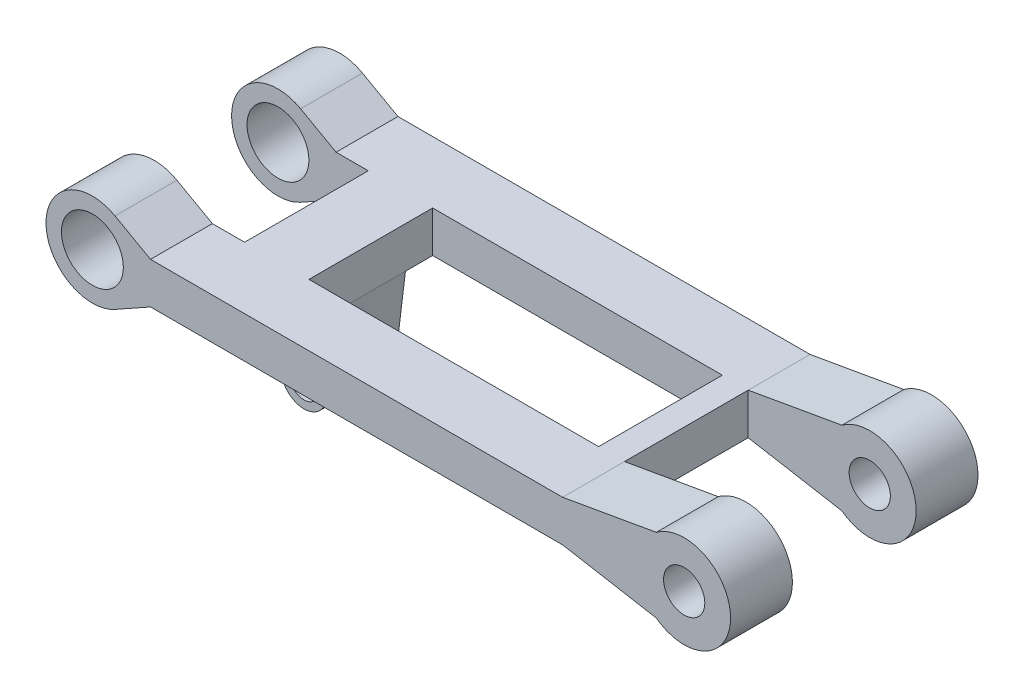
SolidWorks part; units mm, degrees
ref_plane "Front Plane" through (0, 0, 0) normal (0, 0, 1) x (1, 0, 0)
ref_plane "Top Plane" through (0, 0, 0) normal (0, 1, 0) x (1, 0, 0)
ref_plane "Right Plane" through (0, 0, 0) normal (1, 0, 0) x (0, 0, -1)
sketch "Sketch1" plane through (0, 0, 0) normal (0, 0, 1) x (1, 0, 0)
  line L0 (96.1875, 13.7294) -> (96.0241, 23.3011) construction
  line L5 (0, 10) -> (-75, 10) construction
  line L6 (124.8638, 10) -> (0, 10) construction
  line L7 (0, 10) -> (-124.8638, 10) construction
  line L8 (0, 10) -> (75, 10)
  line L9 (75, 10) -> (120.4535, 18.0007)
  line L10 (0, -10) -> (75, -10)
  line L11 (0, 0) -> (0, 10) construction
  line L12 (0, 10) -> (0, 0) construction
  line L13 (0, 0) -> (0, -10) construction
  line L14 (75, -10) -> (120.4535, -18.0007)
  line L15 (-124.8638, 10) -> (-142.0628, 19.6314)
  line L16 (-124.8638, -10) -> (-142.0628, -19.6314)
  line L17 (-124.8638, -10) -> (0, -10)
  line L18 (0, 10) -> (-124.8638, 10)
  arc A1 (120.4535, -18.0007) -> (120.4535, 18.0007) centre (133.9526, 0) ccw
  circle A2 centre (133.9526, 0) radius 10
  circle A4 centre (-153.0564, 0) radius 15
  circle A5 centre (-153.0564, 0) radius 22.5
  point P0 (0, 0)
  dimension "D2" = 22.5
  dimension "D3" = 30
  dimension "D5" = 45
  dimension "D1" = 75
  dimension "D4" = 20
extrude "Boss-Extrude1" add sketch "Sketch1" along normal blind 120
sketch "Sketch2" plane through (0, 10, 0) normal (0, 1, 0) x (1, 0, 0)
  line L0 (-124.8638, -60) -> (-124.8638, -30)
  line L1 (-124.8638, -120) -> (-124.8638, 0) construction
  line L2 (-124.8638, -60) -> (-124.8638, -90)
  line L3 (-124.8638, -90) -> (-189.6321, -90)
  line L4 (-189.6321, -90) -> (-189.6321, -30)
  line L5 (-189.6321, -30) -> (62.4424, -30)
  line L6 (62.4424, -30) -> (62.4424, -90)
  line L7 (62.4424, -90) -> (-191.8997, -90)
  line M4 (-124.8638, 0) -> (-124.8638, -120)
  dimension "D1" = 30
  dimension "D2" = 30
extrude "Cut-Extrude1" cut sketch "Sketch2" against normal mid plane 90 contours L5 L4 L3 M4 | L7 L6 L5 M4
sketch "Sketch3" plane through (0, 0, 120) normal (0, 0, 1) x (1, 0, 0)
  line L0 (-109.2539, -10) -> (-93.6439, -10) construction
  line L1 (-124.8638, -10) -> (75, -10) construction
  line L2 (-93.6439, -10) -> (-93.6439, -47.8166) construction
  line L3 (-104.6439, -47.8166) -> (-109.2539, -10)
  line L4 (-109.2539, -10) -> (-93.6439, -10) construction
  line L5 (-93.6439, -10) -> (-78.0339, -10) construction
  line L6 (-93.6439, -10) -> (-109.2539, -10) construction
  line L7 (-78.0339, -10) -> (-82.6439, -47.8166)
  circle A0 centre (-93.6439, -47.8166) radius 7.2
  circle A1 centre (-93.6439, -47.8166) radius 11
  line M5 (-124.8638, -10) -> (75, -10)
  dimension "D1" = 37.8166
extrude "Boss-Extrude2" add sketch "Sketch3" against normal up to surface (120 mm away) contours A1 L7 L3 M5 | A1 A0 up to face at (-17.5551, 0, 0)
sketch "Sketch4" plane through (62.4424, 0, 0) normal (-1, 0, 0) x (0, 0, 1)
  line L0 (60, 10) -> (60, -58.8166) construction
  line L1 (120, 10) -> (0, 10) construction
  line L2 (0, -58.8166) -> (120, -58.8166) construction
  line L3 (60, -58.8166) -> (0, -58.8166) construction
  line L4 (60, -58.8166) -> (120, -58.8166) construction
  line L5 (120, -58.8166) -> (120, -10) construction
  line L6 (120, -10) -> (0, -10) construction
  line L7 (0, -10) -> (0, -58.8166) construction
  line L8 (43.2, -10) -> (-9.1853, -10)
  line L9 (43.2, -10) -> (76.8, -10)
  line L10 (43.2, -10) -> (43.2, -58.8166)
  line L11 (43.2, -58.8166) -> (76.8, -58.8166)
  line L12 (76.8, -10) -> (76.8, -58.8166)
  line L13 (-9.1853, -10) -> (-9.1853, -58.8166)
  line L14 (-9.1853, -58.8166) -> (43.2, -58.8166)
  line L15 (76.8, -58.8166) -> (133.9662, -58.8166)
  line L16 (133.9662, -58.8166) -> (133.9662, -10)
  line L17 (133.9662, -10) -> (76.8, -10)
  point P18 (60, -10)
  line M1 (30, -10) -> (90, -10)
  dimension "D1" = 33.6
extrude "Cut-Extrude2" cut sketch "Sketch4" along normal blind 180 contours L13 L14 L10 L8 M1 | L16 L17 L12 L15 M1
sketch "Sketch5" plane through (0, -10, 0) normal (0, 1, 0) x (1, 0, 0)
  line L1 (-109.2539, -43.2) -> (-78.0339, -43.2)
  line L2 (-109.2539, -43.2) -> (-109.2539, -76.8)
  line L3 (-109.2539, -76.8) -> (-78.0339, -76.8)
  line L4 (-78.0339, -43.2) -> (-78.0339, -76.8)
extrude "Boss-Extrude3" add sketch "Sketch5" along normal up to surface (20 mm away) up to face at (-28.0713, 10, 60)
sketch "Sketch6" plane through (0, 0, 43.2) normal (0, 0, -1) x (-1, 0, 0)
  line L0 (109.2539, -10) -> (104.6439, -47.8166) construction
  line L1 (78.0339, 10) -> (109.2539, 10)
  line L2 (78.0339, 10) -> (78.0339, -10)
  line L3 (78.0339, -10) -> (109.2539, -10)
  line L4 (109.2539, 10) -> (109.2539, -10)
  line L5 (124.8638, -10) -> (-75, -10) construction
extrude "Boss-Extrude4" add sketch "Sketch6" along normal up to surface (13.2 mm away) up to face at (-138.0564, 0, 30)
sketch "Sketch7" plane through (0, 0, 76.8) normal (0, 0, 1) x (1, 0, 0)
  line L0 (-124.8638, -10) -> (75, -10) construction
  line L1 (-109.4102, -10) -> (-78.0339, -10)
  line L2 (-109.4102, -10) -> (-109.4102, 10)
  line L3 (-109.4102, 10) -> (-78.0339, 10)
  line L4 (-78.0339, -10) -> (-78.0339, 10)
sketch "Sketch8" plane through (0, 0, 90) normal (0, 0, -1) x (-1, 0, 0)
  line L1 (78.0339, 10) -> (109.2539, 10)
  line L2 (78.0339, 10) -> (78.0339, -10)
  line L3 (78.0339, -10) -> (109.2539, -10)
  line L4 (109.2539, 10) -> (109.2539, -10)
extrude "Boss-Extrude5" add sketch "Sketch8" along normal up to surface (13.2 mm away) up to face at (-86.4439, -47.8166, 76.8)
sketch "Sketch9" plane through (0, 10, 0) normal (0, 1, 0) x (1, 0, 0)
  line L0 (75, -60) -> (169.3946, -60) construction
  line L1 (75, -120) -> (75, 0) construction
  line L2 (156.4526, -30) -> (156.4526, -60)
  line L3 (156.4526, -120) -> (156.4526, 0) construction
  line L4 (156.4526, -30) -> (75, -30)
  line L5 (75, -30) -> (75, -90)
  line L6 (75, -90) -> (156.4526, -90)
  line L7 (156.4526, -90) -> (156.4526, -60)
  line M16 (75, -120) -> (75, 0)
  dimension "D1" = 30
extrude "Cut-Extrude3" cut sketch "Sketch9" against normal mid plane 80 contours L5 L0 L2 L4 | L0 L6 L7 M16
